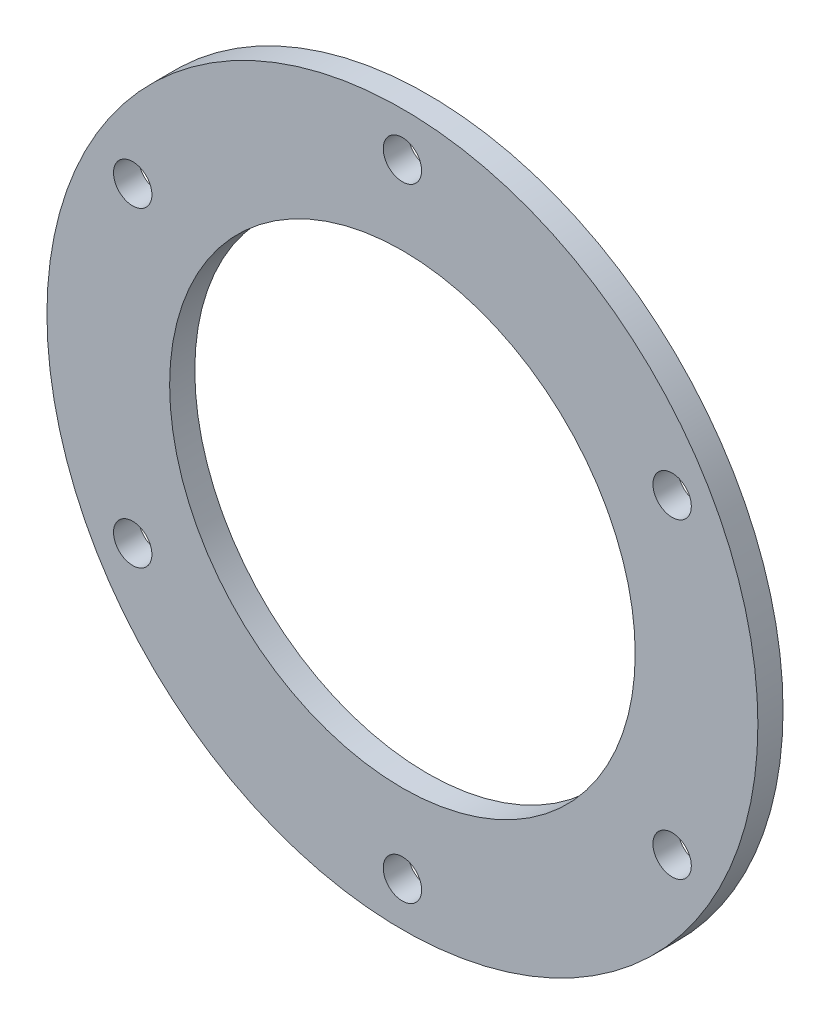
SolidWorks part; units mm, degrees
material "Thornel Mat VMA"
ref_plane "前视基准面" through (0, 0, 0) normal (0, 0, 1) x (1, 0, 0)
ref_plane "上视基准面" through (0, 0, 0) normal (0, 1, 0) x (1, 0, 0)
ref_plane "右视基准面" through (0, 0, 0) normal (1, 0, 0) x (0, 0, -1)
sketch "草图1" plane through (0, 0, 0) normal (0, 0, 1) x (1, 0, 0)
  circle A0 centre (0, 0) radius 28.25
  circle A1 centre (0, 0) radius 18.5
  dimension "D1" = 56.5
  dimension "D2" = 37
extrude "凸台-拉伸1" add sketch "草图1" along normal blind 2
sketch "草图2" plane through (0, 0, 2) normal (0, 0, 1) x (1, 0, 0)
  circle A0 centre (0, 0) radius 24.75 construction
  circle A1 centre (0, 24.75) radius 1.525
  circle A2 centre (21.4341, 12.375) radius 1.525
  circle A3 centre (21.4341, -12.375) radius 1.525
  circle A4 centre (0, -24.75) radius 1.525
  circle A5 centre (-21.4341, -12.375) radius 1.525
  circle A6 centre (-21.4341, 12.375) radius 1.525
  point P5 (-31.3011, 12.5247)
  point P6 (0, 0)
  point P18 (0, 0)
  dimension "D1" = 49.5
  dimension "D2" = 3.05
  dimension "D3" = 6
extrude "切除-拉伸1" cut sketch "草图2" against normal blind 2
